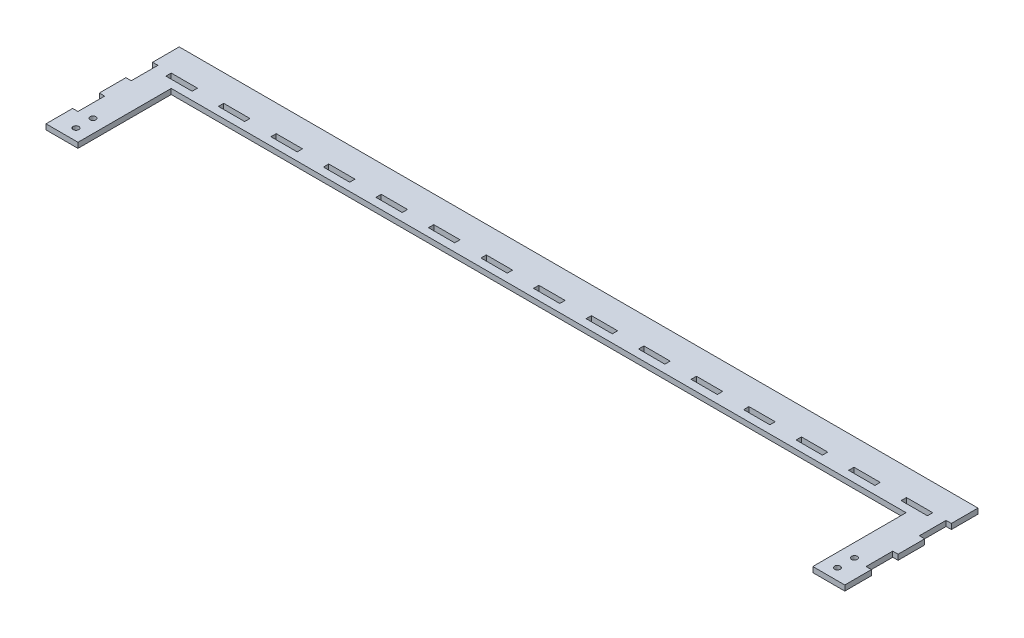
SolidWorks part; units mm, degrees
ref_plane "Front Plane" through (0, 0, 0) normal (0, 0, 1) x (1, 0, 0)
ref_plane "Top Plane" through (0, 0, 0) normal (0, 1, 0) x (1, 0, 0)
ref_plane "Right Plane" through (0, 0, 0) normal (1, 0, 0) x (0, 0, -1)
sketch "Sketch1" plane through (0, 0, 0) normal (0, 1, 0) x (1, 0, 0)
  line L0 (0, -26.4292) -> (0, 52.5615) construction
  line L1 (299.8, 24) -> (299.8, 4)
  line L2 (285.8, -44.149) -> (285.8, -73.2727) construction
  line L3 (299.8, -76) -> (275.8, -76)
  line L4 (275.8, -76) -> (275.8, -6)
  line L5 (275.8, -6) -> (-275.8, -6)
  line L6 (-9.8625, 0) -> (9.8625, 0)
  line L7 (9.8625, 0) -> (9.8625, 4)
  line L8 (9.8625, 4) -> (-9.8625, 4)
  line L9 (29.5875, 4) -> (29.5875, 0)
  line L10 (29.5875, 0) -> (49.3125, 0)
  line L11 (49.3125, 0) -> (49.3125, 4)
  line L12 (49.3125, 4) -> (29.5875, 4)
  line L13 (88.7325, 4) -> (69.0075, 4)
  line L14 (69.0075, 4) -> (69.0075, 0)
  line L15 (69.0075, 0) -> (88.7325, 0)
  line L16 (88.7325, 0) -> (88.7325, 4)
  line L17 (128.1525, 4) -> (108.4275, 4)
  line L18 (108.4275, 4) -> (108.4275, 0)
  line L19 (108.4275, 0) -> (128.1525, 0)
  line L20 (128.1525, 0) -> (128.1525, 4)
  line L21 (167.5725, 4) -> (147.8475, 4)
  line L22 (147.8475, 4) -> (147.8475, 0)
  line L23 (147.8475, 0) -> (167.5725, 0)
  line L24 (167.5725, 0) -> (167.5725, 4)
  line L25 (206.9925, 4) -> (187.2675, 4)
  line L26 (187.2675, 4) -> (187.2675, 0)
  line L27 (187.2675, 0) -> (206.9925, 0)
  line L28 (206.9925, 0) -> (206.9925, 4)
  line L29 (246.4125, 4) -> (226.6875, 4)
  line L30 (226.6875, 4) -> (226.6875, 0)
  line L31 (226.6875, 0) -> (246.4125, 0)
  line L32 (246.4125, 0) -> (246.4125, 4)
  line L33 (285.8325, 4) -> (266.1075, 4)
  line L34 (266.1075, 4) -> (266.1075, 0)
  line L35 (266.1075, 0) -> (285.8325, 0)
  line L36 (285.8325, 0) -> (285.8325, 4)
  line L37 (299.8, 4) -> (295.8, 4)
  line L38 (295.8, 4) -> (295.8, -16)
  line L39 (299.8, 24) -> (-299.8, 24)
  line L40 (295.8, -16) -> (299.8, -16)
  line L41 (299.8, -16) -> (299.8, -36)
  line L42 (299.8, -36) -> (295.8, -36)
  line L43 (295.8, -36) -> (295.8, -56)
  line L44 (295.8, -56) -> (299.8, -56)
  line L45 (299.8, -56) -> (299.8, -76)
  line L46 (-285.8, -44.149) -> (-285.8, -73.2727) construction
  line L47 (-299.8, -56) -> (-299.8, -76)
  line L48 (-295.8, -56) -> (-299.8, -56)
  line L49 (-295.8, -36) -> (-295.8, -56)
  line L50 (-299.8, -36) -> (-295.8, -36)
  line L51 (-299.8, -16) -> (-299.8, -36)
  line L52 (-295.8, -16) -> (-299.8, -16)
  line L53 (-295.8, 4) -> (-295.8, -16)
  line L54 (-299.8, 4) -> (-295.8, 4)
  line L55 (-285.8325, 0) -> (-285.8325, 4)
  line L56 (-266.1075, 0) -> (-285.8325, 0)
  line L57 (-266.1075, 4) -> (-266.1075, 0)
  line L58 (-285.8325, 4) -> (-266.1075, 4)
  line L59 (-246.4125, 0) -> (-246.4125, 4)
  line L60 (-226.6875, 0) -> (-246.4125, 0)
  line L61 (-226.6875, 4) -> (-226.6875, 0)
  line L62 (-246.4125, 4) -> (-226.6875, 4)
  line L63 (-206.9925, 0) -> (-206.9925, 4)
  line L64 (-187.2675, 0) -> (-206.9925, 0)
  line L65 (-187.2675, 4) -> (-187.2675, 0)
  line L66 (-206.9925, 4) -> (-187.2675, 4)
  line L67 (-167.5725, 0) -> (-167.5725, 4)
  line L68 (-147.8475, 0) -> (-167.5725, 0)
  line L69 (-147.8475, 4) -> (-147.8475, 0)
  line L70 (-167.5725, 4) -> (-147.8475, 4)
  line L71 (-128.1525, 0) -> (-128.1525, 4)
  line L72 (-108.4275, 0) -> (-128.1525, 0)
  line L73 (-108.4275, 4) -> (-108.4275, 0)
  line L74 (-128.1525, 4) -> (-108.4275, 4)
  line L75 (-88.7325, 0) -> (-88.7325, 4)
  line L76 (-69.0075, 0) -> (-88.7325, 0)
  line L77 (-69.0075, 4) -> (-69.0075, 0)
  line L78 (-88.7325, 4) -> (-69.0075, 4)
  line L79 (-49.3125, 4) -> (-29.5875, 4)
  line L80 (-49.3125, 0) -> (-49.3125, 4)
  line L81 (-29.5875, 0) -> (-49.3125, 0)
  line L82 (-29.5875, 4) -> (-29.5875, 0)
  line L83 (-9.8625, 0) -> (-9.8625, 4)
  line L84 (-275.8, -76) -> (-275.8, -6)
  line L85 (-299.8, -76) -> (-275.8, -76)
  line L86 (-299.8, 24) -> (-299.8, 4)
  circle A0 centre (285.8, -67.5) radius 2.125
  circle A1 centre (285.8, -54.75) radius 2.125
  circle A2 centre (-285.8, -54.75) radius 2.125
  circle A3 centre (-285.8, -67.5) radius 2.125
  point P69 (0, 24)
  point P100 (0, 4)
  point P101 (0, 0)
  point P102 (0, -6)
  dimension "D11" = 4.25
  dimension "D1" = 24
  dimension "D2" = 10
  dimension "D3" = 299.8
  dimension "D4" = 24
  dimension "D5" = 6
  dimension "D6" = 9.8625
  dimension "D7" = 4
  dimension "D8" = 19.725
  dimension "D9" = 19.725
  dimension "D12" = 8.5
  dimension "D13" = 12.75
  dimension "D14" = 100
  dimension "D15" = 20
  dimension "D16" = 4
  dimension "D10" = 7
extrude "Boss-Extrude1" add sketch "Sketch1" along normal blind 4
